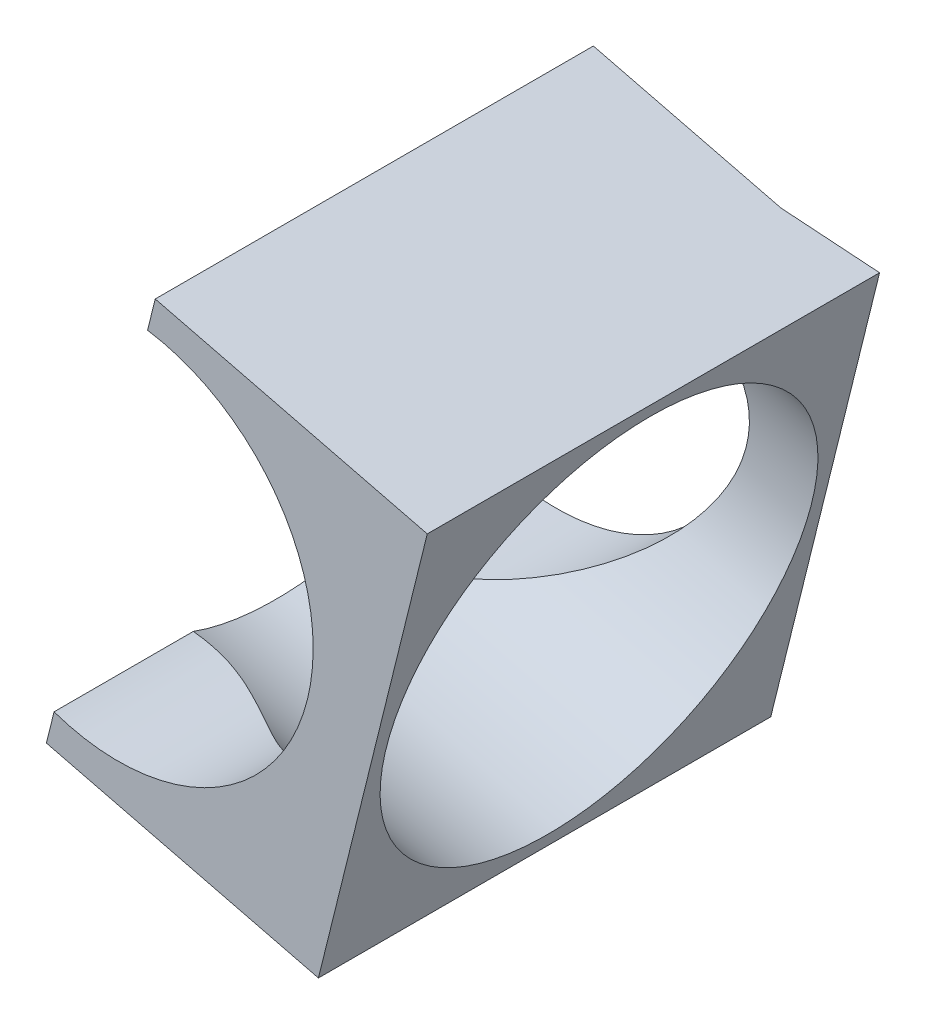
SolidWorks part; units mm, degrees
material "PC Alta Viscosidade"
ref_plane "Plano frontal" through (0, 0, 0) normal (0, 0, 1) x (1, 0, 0)
ref_plane "Plano superior" through (0, 0, 0) normal (0, 1, 0) x (1, 0, 0)
ref_plane "Plano direito" through (0, 0, 0) normal (1, 0, 0) x (0, 0, -1)
sketch "Esboço1" plane through (0, 0, 0) normal (0, 0, 1) x (1, 0, 0)
  line L0 (17.4331, 13.8142) -> (2.0973, 17.616)
  line L1 (2.0973, 17.616) -> (1.6653, 15.8732)
  line L2 (17.4331, 13.8142) -> (27.6246, 11.2876) construction
  line L3 (11.2972, -10.9366) -> (-4.0386, -7.1348)
  line L4 (-4.0386, -7.1348) -> (-3.6065, -5.392)
  line L5 (11.2972, -10.9366) -> (21.4887, -13.4631) construction
  line L6 (17.4331, 13.8142) -> (11.2972, -10.9366)
  circle A0 centre (0, 5) radius 11 construction
  arc A1 (-3.6065, -5.392) -> (1.6653, 15.8732) centre (0, 5) ccw
  point P9 (0, 5)
  dimension "D1" = 1
extrude "Ressalto-extrusão1" add sketch "Esboço1" against normal up to surface (25.5 mm away)
sketch "Esboço2" plane through (4.2357, 17.0859, 0) normal (0.2406, 0.9706, 0) x (0, 0, 1)
  line L0 (-24.7, -2.2031) -> (-24.7, 8.6969)
  line L1 (-25.5, -2.2031) -> (0, -2.2031) construction
  line L2 (-24.7, 9.7969) -> (-24.7, -12.2031) construction
  line L3 (-24.7, 8.6969) -> (-25.5, 13.5969)
  line L4 (-25.5, 13.5969) -> (0, 13.5969) construction
  line L5 (-24.7, -2.2031) -> (-25.5, -2.2031)
  line L6 (-25.5, -2.2031) -> (-25.5, 13.5969)
  dimension "D1" = 4.9
extrude "Corte-extrusão1" cut sketch "Esboço2" against normal through all
sketch "Esboço3" plane through (13.1974, -3.2717, 0) normal (0.9706, -0.2406, 0) x (-0.2406, -0.9706, 0)
  arc A0 (-16.7364, 11.0804) -> (-4.8531, 0.75) centre (-4.8531, 12.75) ccw construction
  circle A1 centre (-4.8531, 12.75) radius 12
extrude "Corte-extrusão2" cut sketch "Esboço3" against normal through all
